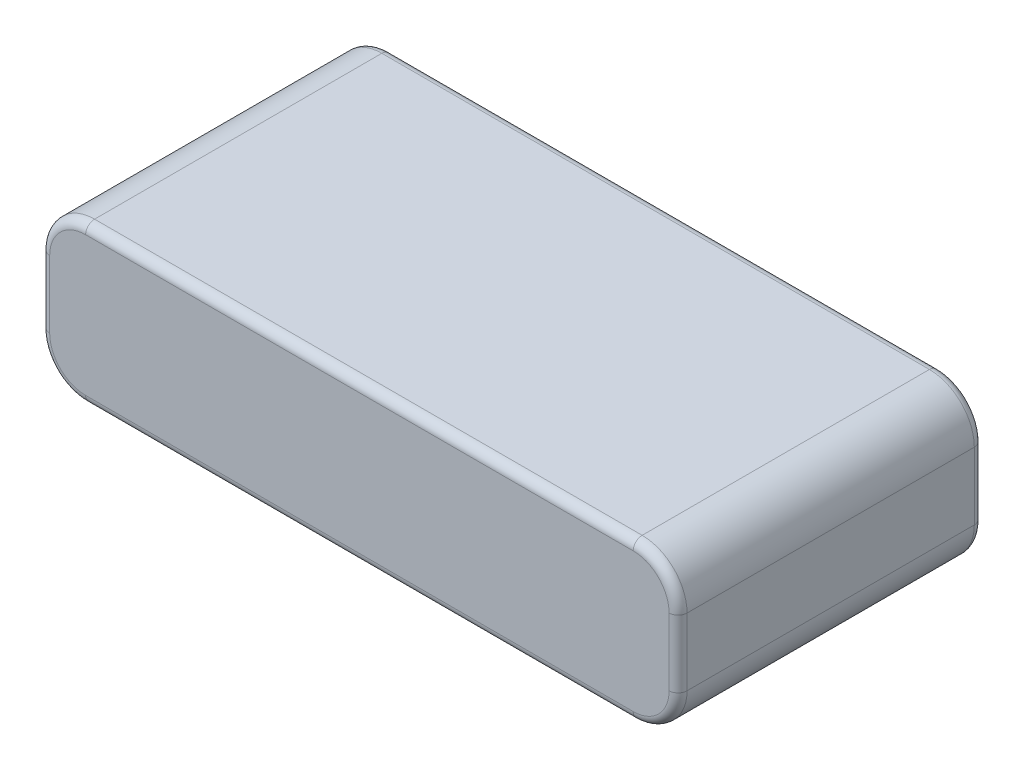
SolidWorks part; units mm, degrees
ref_plane "Front Plane" through (0, 0, 0) normal (0, 0, 1) x (1, 0, 0)
ref_plane "Top Plane" through (0, 0, 0) normal (0, 1, 0) x (1, 0, 0)
ref_plane "Right Plane" through (0, 0, 0) normal (1, 0, 0) x (0, 0, -1)
sketch "Sketch1" plane through (0, 0, 0) normal (0, 1, 0) x (1, 0, 0)
  line L1 (-35.5, -17) -> (35.5, -17)
  line L2 (-35.5, -17) -> (-35.5, 17)
  line L3 (-35.5, 17) -> (35.5, 17)
  line L4 (35.5, -17) -> (35.5, 17)
  line L5 (-35.5, -17) -> (35.5, 17) construction
  line L6 (-35.5, 17) -> (35.5, -17) construction
  point P0 (0, 0)
  dimension "D1" = 71
  dimension "D2" = 34
extrude "Boss-Extrude1" add sketch "Sketch1" along normal blind 17.5
fillet "Fillet1" radius 5 4 edges at (35.5, 0, 0) (35.5, 17.5, 0) (-35.5, 17.5, 0) (-35.5, 0, 0)
fillet "Fillet2" radius 1 16 edges at (34.0355, 16.0355, -17) (0, 17.5, -17) (-34.0355, 16.0355, -17) (-35.5, 8.75, -17) (-34.0355, 1.4645, -17) (0, 0, -17) (34.0355, 1.4645, -17) (35.5, 8.75, -17) (-34.0355, 1.4645, 17) (-35.5, 8.75, 17) (-34.0355, 16.0355, 17) (0, 17.5, 17) (34.0355, 16.0355, 17) (35.5, 8.75, 17) (34.0355, 1.4645, 17) (0, 0, 17)
sketch "Sketch4" plane through (0, 0, 0) normal (0, -1, 0) x (1, 0, 0)
  text T0 "ARIFUL-44" font "Century Gothic" height 5.5
extrude "Boss-Extrude3" add sketch "Sketch4" along normal blind 0.5
